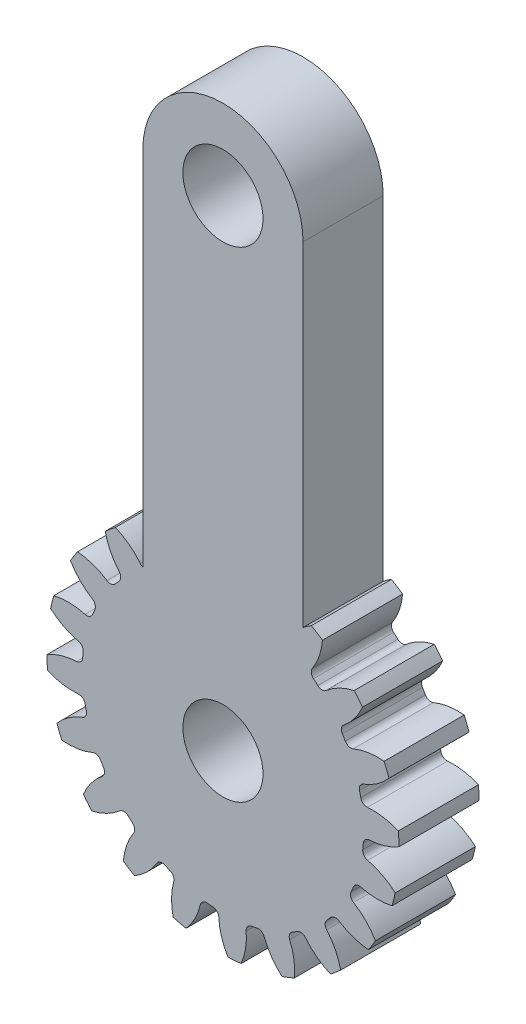
SolidWorks part; units mm, degrees
material "ABS"
ref_plane "Front" through (0, 0, 0) normal (0, 0, 1) x (1, 0, 0)
ref_plane "Top" through (0, 0, 0) normal (0, 1, 0) x (1, 0, 0)
ref_plane "Right" through (0, 0, 0) normal (1, 0, 0) x (0, 0, -1)
sketch "Sketch3" plane through (0, 0, 0) normal (0, 0, 1) x (1, 0, 0)
  circle A0 centre (0, 0) radius 27.94
  dimension "od" = 55.88
extrude "gearBody" add sketch "Sketch3" along normal blind 12.7
sketch "Sketch2" plane through (0, 0, 0) normal (0, 0, 1) x (1, 0, 0)
  line L0 (0, 0) -> (22.7191, 9.4105) construction
  line L1 (29.8471, -9.3212) -> (0, 0) construction
  line L2 (0, 0) -> (36.3143, 0) construction
  line L3 (25.3982, -0.3053) -> (25.0293, -4.3236) construction
  line L5 (25.2137, -2.3145) -> (0, 0) construction
  line L7 (0, 0) -> (24.591, 0) construction
  arc A0 (24.586, -0.4935) -> (24.265, -3.9907) centre (0, 0) ccw construction
  arc A1 (27.929, 0.7831) -> (27.3197, -5.8547) centre (0, 0) ccw construction
  arc A2 (25.3982, -0.3053) -> (25.0293, -4.3236) centre (0, 0) ccw construction
  arc A3 (22.162, -2.4879) -> (22.2446, -1.5884) centre (0, 0) ccw
  arc A4 (29.8471, -9.3212) -> (22.9306, -3.5779) centre (20.6262, -13.3894) ccw
  arc A5 (29.8471, -9.3212) -> (31.0453, 3.7316) centre (0, 0) ccw
  arc A6 (31.0453, 3.7316) -> (23.1988, -0.6565) centre (22.7191, 9.4105) cw
  arc A7 (22.2446, -1.5884) -> (23.1988, -0.6565) centre (23.2466, -1.66) cw
  arc A8 (22.9306, -3.5779) -> (22.162, -2.4879) centre (23.1603, -2.5999) cw
  point P6 (31.0453, 3.7316)
  point P22 (29.8471, -9.3212)
  dimension "baseDia" = 49.1819
  dimension "od" = 55.88
  dimension "pd" = 50.8
  dimension "rd" = 44.6024
  dimension "rFillet" = 1.0046
  dimension "pointX" = 31.0453
  dimension "pointY" = 3.7316
  dimension "CTT" = 4.0183
  dimension "flankCenterAngle" = 22.5
extrude "toothCut" cut sketch "Sketch2" along normal through all
pattern_circular "CirPattern1" count 20 over 360 about axis through (0, 0, 0) along (0, 0, 1) of "toothCut"
sketch "boreDia" plane through (0, 0, 0) normal (0, 0, 1) x (1, 0, 0)
  circle A0 centre (0, 0) radius 6.35
  dimension "boreDia" = 12.7
extrude "bore" cut sketch "boreDia" against normal mid plane 25400
sketch3d "3DSketch1" plane through (0, 0, 0) normal (0, 0, 1) x (1, 0, 0)
sketch "Sketch4" plane through (0, 0, 0) normal (0, 0, 1) x (1, 0, 0)
  line L0 (0, 0) -> (0, 76.2) construction
  line L1 (12.7, 18.3318) -> (12.7, 76.2)
  line L2 (-12.7, 18.3318) -> (-12.7, 76.2)
  line L3 (12.7, 76.2) -> (-12.7, 76.2) construction
  circle A0 centre (0, 0) radius 22.3012 construction
  arc A1 (-9.2145, -20.3085) -> (-8.3846, -20.665) centre (0, 0) ccw construction
  circle A2 centre (0, 76.2) radius 6.35
  arc A3 (12.7, 76.2) -> (-12.7, 76.2) centre (0, 76.2) ccw
  arc A4 (12.7, 18.3318) -> (-12.7, 18.3318) centre (0, 0) ccw
  point P1 (75.3022, -12.3173)
  point P11 (0, 76.2)
  point P15 (0, 0)
  point P16 (42.8936, 62.9808)
  point P17 (42.8936, 62.9808)
  dimension "D3" = 12.7
  dimension "D1" = 25.4
  dimension "D2" = 76.2
extrude "Boss-Extrude1" add sketch "Sketch4" along normal blind 12.7
